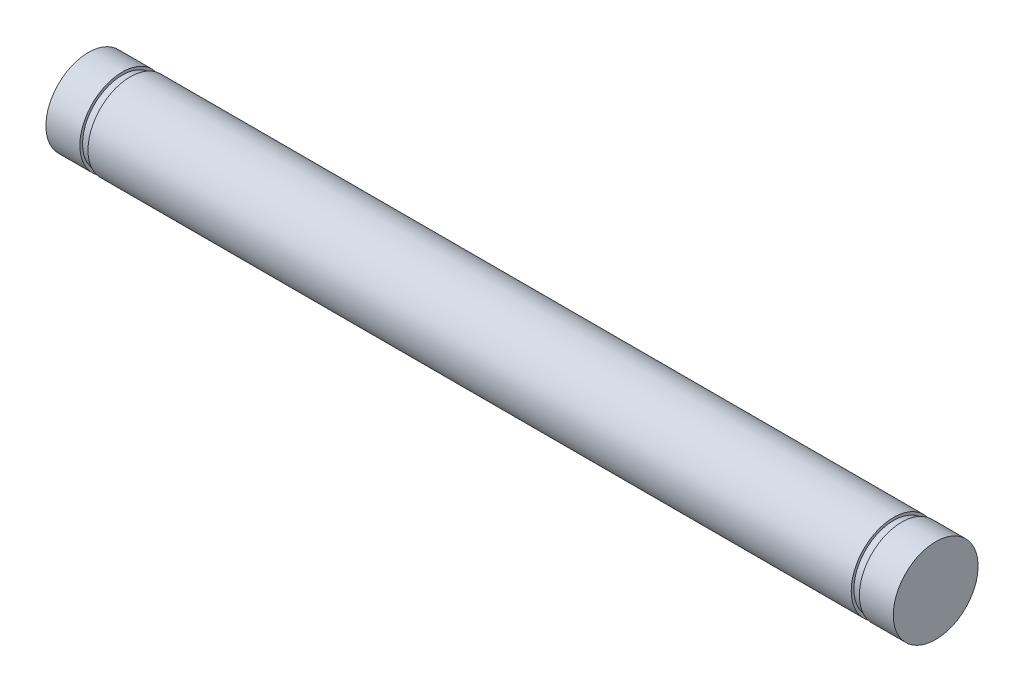
SolidWorks part; units mm, degrees
material "A-Glass Fiber"
ref_plane "Front" through (0, 0, 0) normal (0, 0, 1) x (1, 0, 0)
ref_plane "Top" through (0, 0, 0) normal (0, 1, 0) x (1, 0, 0)
ref_plane "Right" through (0, 0, 0) normal (1, 0, 0) x (0, 0, -1)
sketch "Sketch1" plane through (0, 0, 0) normal (0, 0, 1) x (1, 0, 0)
  line L0 (-25.4, 0) -> (25.4, 0) construction
  line L1 (25.4, 1.5875) -> (25.4, -1.5875) construction
  line L2 (-25.4, 1.5875) -> (-25.4, -1.5875) construction
  dimension "Length" = 50.8
  dimension "Diameter" = 3.175
sketch "Sketch2" plane through (0, 0, 0) normal (1, 0, 0) x (0, 0, -1)
  circle A0 centre (0, 0) radius 1.5875
extrude "Extrude1" add sketch "Sketch2" against normal up to vertex (25.4 mm away) and the other way up to vertex (25.4 mm away) up to point (-25.4, 1.5875, 0) other way up to point (25.4, 1.5875, 0)
chamfer "Chamfer1" distance 0.3175 angle 45 2 edges at (25.4, 0, -1.5875) (-25.4, 0, -1.5875)
ref_plane "Plane1" through (-22.225, 0, 0) normal (-1, 0, 0) x (0, 0, 1)
sketch "Sketch3" plane through (-22.225, 0, 0) normal (-1, 0, 0) x (0, 0, 1)
  circle A0 centre (0, 0) radius 1.4859
  dimension "D1" = 2.9718
extrude "Cut-Extrude1" cut sketch "Sketch3" along normal blind 0.3048 flip side to cut
ref_plane "Plane2" through (6.35, 0, 0) normal (-1, 0, 0) x (0, 0, 1)
sketch "Sketch4" plane through (6.35, 0, 0) normal (-1, 0, 0) x (0, 0, 1)
  circle A0 centre (0, 0) radius 1.4859
  dimension "D1" = 2.9718
extrude "Cut-Extrude2" cut sketch "Sketch4" against normal blind 0.3048 flip side to cut
sketch "Sketch5" plane through (0, 0, 0) normal (0, 0, 1) x (1, 0, 0)
  line L0 (25.4, 0) -> (-25.4, 0) construction
  line L1 (25.4, 3.175) -> (7.9248, 3.175)
  line L2 (25.4, 3.175) -> (25.4, -3.175)
  line L3 (25.4, -3.175) -> (7.9248, -3.175)
  line L4 (7.9248, 3.175) -> (7.9248, -3.175)
  line L5 (-23.7998, 3.175) -> (-25.4, 3.175)
  line L6 (-23.7998, 3.175) -> (-23.7998, -3.175)
  line L7 (-23.7998, -3.175) -> (-25.4, -3.175)
  line L8 (-25.4, 3.175) -> (-25.4, -3.175)
  line L9 (25.4, -1.27) -> (25.4, 1.27) construction
  line L10 (-25.4, 1.27) -> (-25.4, -1.27) construction
  line L11 (-22.5298, -1.5875) -> (-22.5298, 1.5875) construction
  line L12 (6.6548, 1.4859) -> (6.6548, -1.4859) construction
  dimension "D1" = 6.35
  dimension "D2" = 1.27
  dimension "D3" = 1.27
extrude "Cut-Extrude3" cut sketch "Sketch5" against normal through all both and the other way through all
equation "\"D1@Chamfer1\" = \"Diameter@Sketch1\"*.1"
